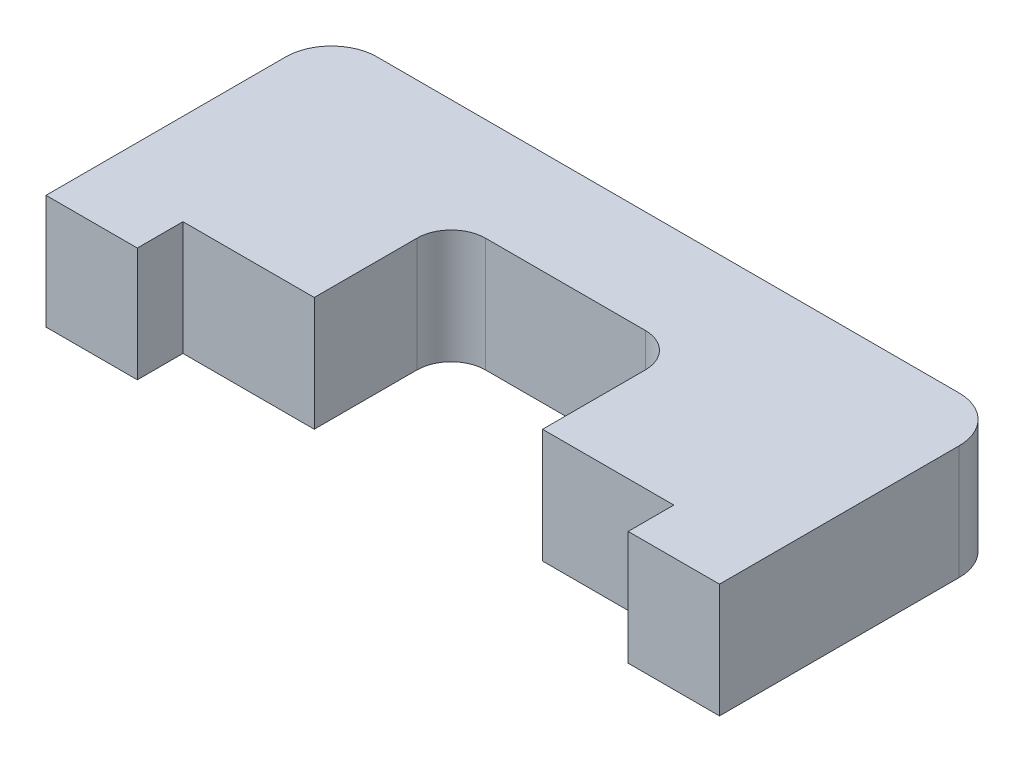
SolidWorks part; units mm, degrees
ref_plane "Front Plane" through (0, 0, 0) normal (0, 0, 1) x (1, 0, 0)
ref_plane "Top Plane" through (0, 0, 0) normal (0, 1, 0) x (1, 0, 0)
ref_plane "Right Plane" through (0, 0, 0) normal (1, 0, 0) x (0, 0, -1)
sketch "Sketch1" plane through (0, 0, 0) normal (0, 1, 0) x (1, 0, 0)
  line L1 (14.75, -6.25) -> (-14.75, -6.25)
  line L2 (14.75, -6.25) -> (14.75, 6.25)
  line L3 (14.75, 6.25) -> (-14.75, 6.25)
  line L4 (-14.75, -6.25) -> (-14.75, 6.25)
  line L5 (14.75, -6.25) -> (-14.75, 6.25) construction
  line L6 (14.75, 6.25) -> (-14.75, -6.25) construction
  point P0 (0, 0)
  dimension "D1" = 12.5
  dimension "D2" = 29.5
extrude "Boss-Extrude1" add sketch "Sketch1" along normal blind 5
sketch "Sketch2" plane through (0, 5, 0) normal (0, 1, 0) x (1, 0, 0)
  line L0 (-5, -6.25) -> (5, -6.25)
  line L1 (-5, -6.25) -> (-5, 1.75)
  line L2 (5, -6.25) -> (5, 1.75)
  line L3 (-5, 1.75) -> (5, 1.75)
  line L4 (-14.75, -6.25) -> (14.75, -6.25) construction
  point P6 (0, -6.25)
  dimension "D1" = 10
  dimension "D2" = 8
extrude "Cut-Extrude1" cut sketch "Sketch2" against normal through all
fillet "Fillet1" radius 2 2 edges at (14.75, 2.5, -6.25) (-14.75, 2.5, -6.25)
fillet "Fillet2" radius 1.5 2 edges at (5, 2.5, -1.75) (-5, 2.5, -1.75)
sketch "Sketch3" plane through (0, 0, 6.25) normal (0, 0, 1) x (1, 0, 0)
  line L0 (-10.75, 5) -> (-10.75, 0)
  line L1 (-10.75, 5) -> (10.75, 5)
  line L2 (-10.75, 0) -> (10.75, 0)
  line L3 (10.75, 5) -> (10.75, 0)
  line L4 (-14.75, 5) -> (-5, 5) construction
  line L5 (-14.75, 0) -> (-5, 0) construction
  line L6 (-14.75, 5) -> (-14.75, 0) construction
  line L7 (14.75, 5) -> (14.75, 0) construction
  dimension "D1" = 4
  dimension "D2" = 4
extrude "Cut-Extrude2" cut sketch "Sketch3" against normal blind 2
